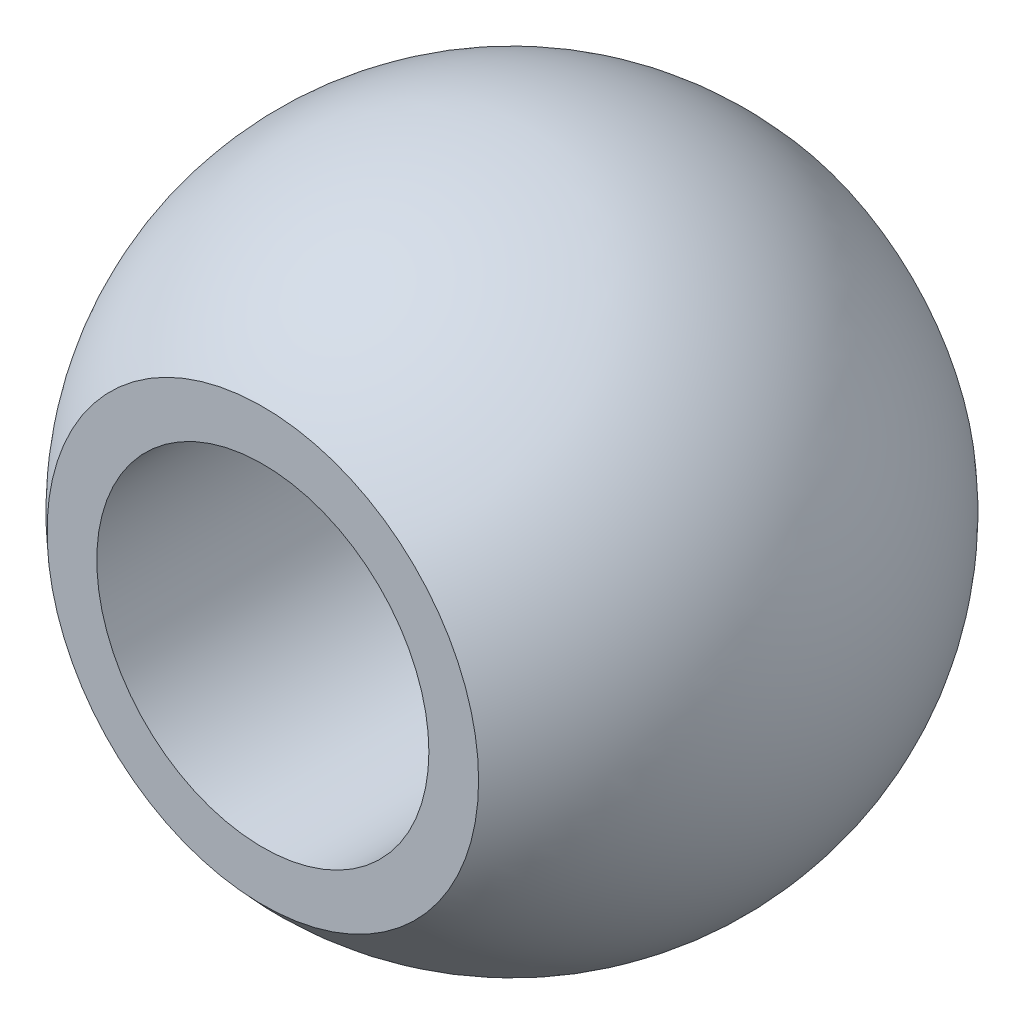
SolidWorks part; units mm, degrees
material "Plain Carbon Steel"
ref_plane "Front Plane" through (0, 0, 0) normal (0, 0, 1) x (1, 0, 0)
ref_plane "Top Plane" through (0, 0, 0) normal (0, 1, 0) x (1, 0, 0)
ref_plane "Right Plane" through (0, 0, 0) normal (1, 0, 0) x (0, 0, -1)
sketch "Sketch1" plane through (0, 0, 0) normal (1, 0, 0) x (0, 0, -1)
  line L0 (0, 0) -> (0, 61.9768) construction
  line L1 (-31.259, 0) -> (29.384, 0) construction
  line L2 (-6, 5.1973) -> (-6, 4)
  line L3 (-6, 4) -> (6, 4)
  line L4 (6, 4) -> (6, 5.1973)
  arc A0 (-6, 5.1973) -> (6, 5.1973) centre (0, 0) cw
  point P7 (0, 7.938)
  dimension "D2" = 7.938
  dimension "D1" = 12
  dimension "D3" = 4
revolve "Revolve1" add sketch "Sketch1"
sketch "Sketch2" plane through (0, 0, 0) normal (1, 0, 0) x (0, 0, -1)
  line L0 (-11.0989, 0) -> (11.0989, 0) construction
  arc A0 (6, 5.1973) -> (-6, 5.1973) centre (0, 0) ccw construction
  point P3 (0, 0)
